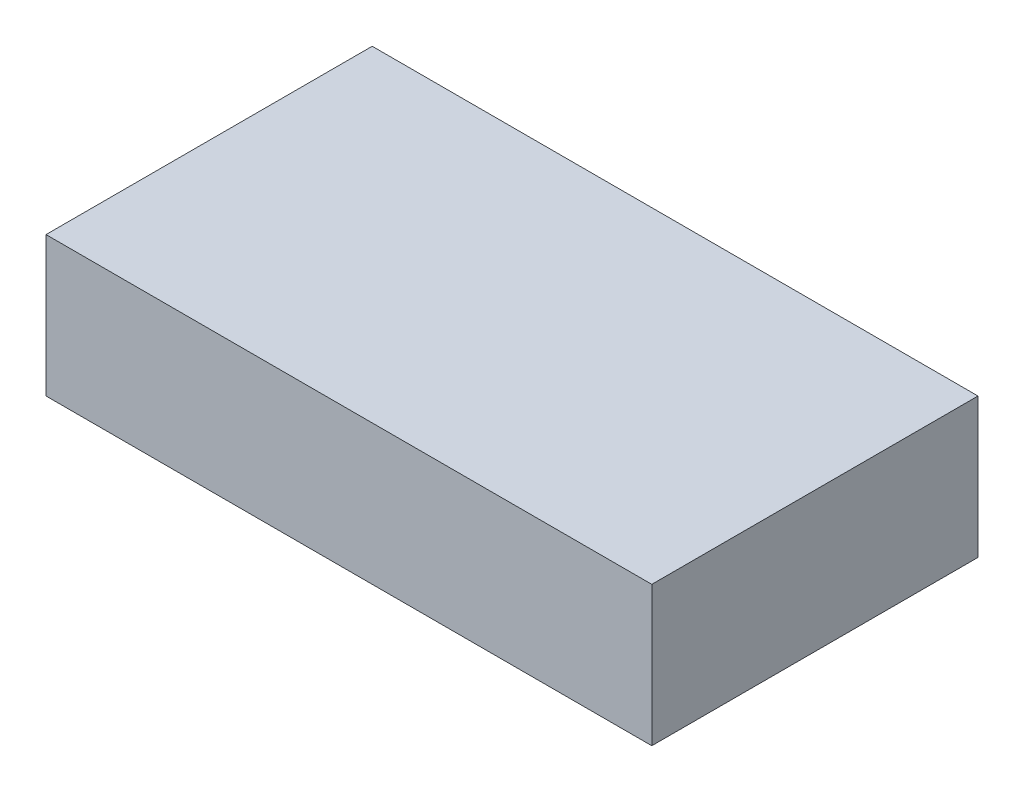
SolidWorks part; units mm, degrees
ref_plane "Front Plane" through (0, 0, 0) normal (0, 0, 1) x (1, 0, 0)
ref_plane "Top Plane" through (0, 0, 0) normal (0, 1, 0) x (1, 0, 0)
ref_plane "Right Plane" through (0, 0, 0) normal (1, 0, 0) x (0, 0, -1)
sketch "Sketch1" plane through (0, 0, 0) normal (0, 1, 0) x (1, 0, 0)
  line L1 (0, 0) -> (165.1, 0)
  line L2 (0, 0) -> (0, -88.9)
  line L3 (0, -88.9) -> (165.1, -88.9)
  line L4 (165.1, 0) -> (165.1, -88.9)
extrude "Boss-Extrude1" add sketch "Sketch1" along normal blind 38.1
sketch "Sketch2" plane through (0, 38.1, 0) normal (0, 1, 0) x (1, 0, 0)
  line L0 (0, -44.45) -> (55.0333, -44.45) construction
  line L1 (0, 0) -> (0, -88.9) construction
  line L2 (55.0333, -44.45) -> (110.0667, -44.45) construction
  line L3 (110.0667, -44.45) -> (165.1, -44.45) construction
  line L4 (165.1, -88.9) -> (165.1, 0) construction
  line L5 (55.0333, 0) -> (55.0333, -88.9) construction
  line L6 (165.1, 0) -> (0, 0) construction
  line L7 (0, -88.9) -> (165.1, -88.9) construction
  line L8 (110.0667, 0) -> (110.0667, -88.9) construction
sketch "Sketch3" plane through (0, 0, 0) normal (0, -1, 0) x (1, 0, 0)
  line L0 (0, 44.45) -> (55.0333, 44.45) construction
  line L1 (55.0333, 44.45) -> (110.0667, 44.45) construction
  line L2 (110.0667, 44.45) -> (165.1, 44.45) construction
  line L3 (55.0333, 88.9) -> (55.0333, 0) construction
  line L4 (110.0667, 88.9) -> (110.0667, 0) construction
